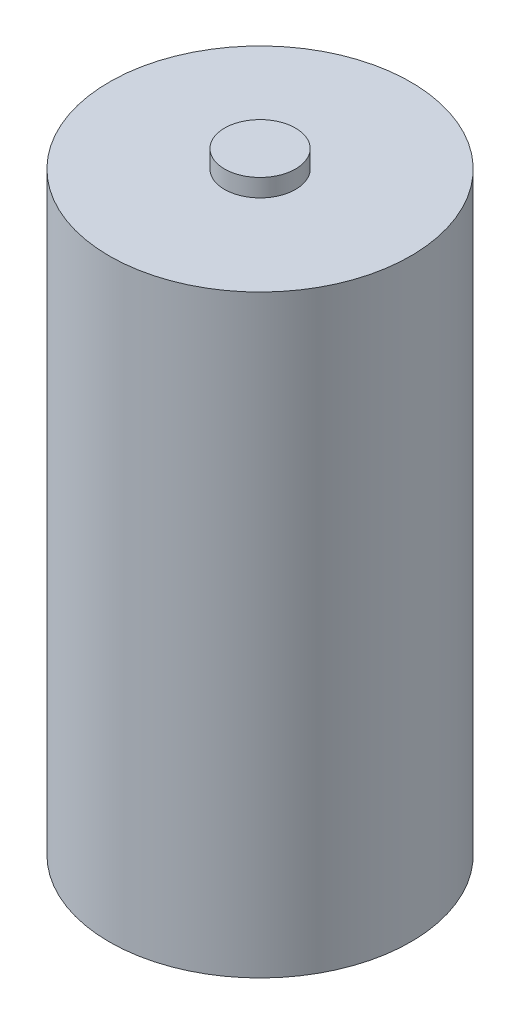
SolidWorks part; units mm, degrees
ref_plane "Front Plane" through (0, 0, 0) normal (0, 0, 1) x (1, 0, 0)
ref_plane "Top Plane" through (0, 0, 0) normal (0, 1, 0) x (1, 0, 0)
ref_plane "Right Plane" through (0, 0, 0) normal (1, 0, 0) x (0, 0, -1)
sketch "Sketch1" plane through (0, 0, 0) normal (0, 0, 1) x (1, 0, 0)
  line L0 (0, 0) -> (-8.5, 0)
  line L1 (-8.5, 0) -> (-8.5, 33.5)
  line L2 (-8.5, 33.5) -> (-2, 33.5)
  line L3 (-2, 33.5) -> (-2, 34.5)
  line L4 (-2, 34.5) -> (0, 34.5)
  line L5 (0, 34.5) -> (0, 0) construction
  line L6 (0, 0) -> (0, 34.5)
  dimension "D1" = 34.5
  dimension "D2" = 1
  dimension "D3" = 8.5
  dimension "D4" = 2
revolve "Revolve1" add sketch "Sketch1" angle 360 about L5
